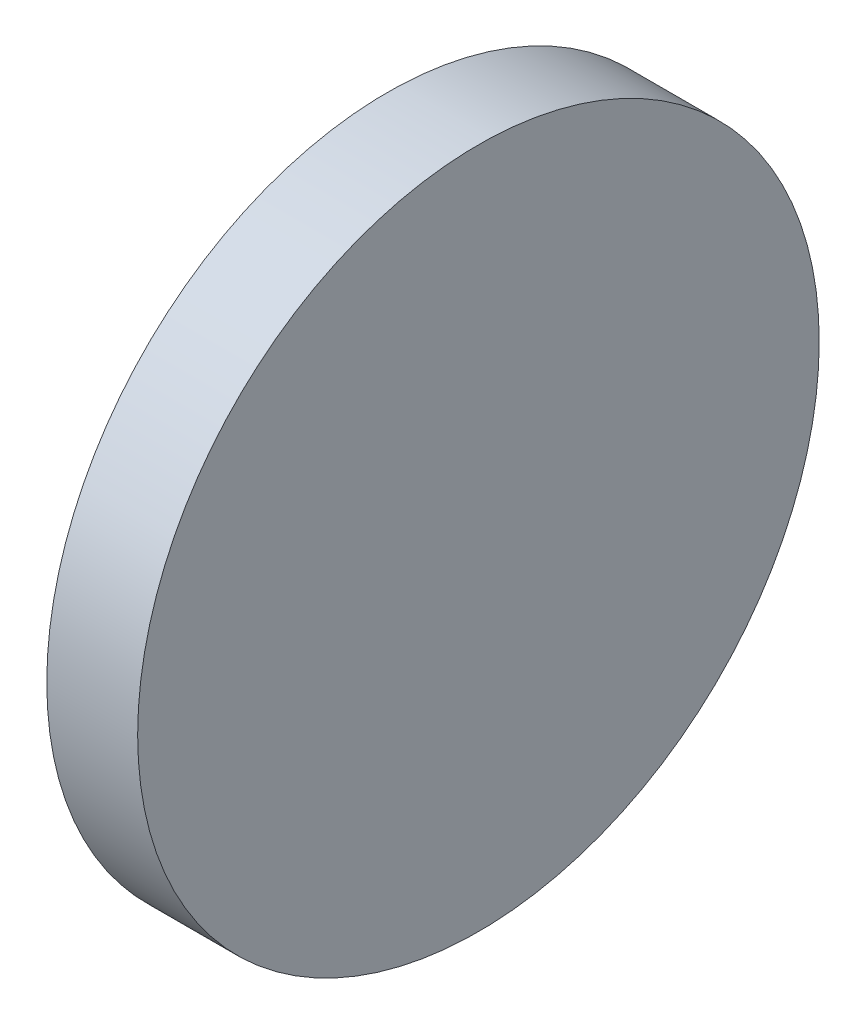
SolidWorks part; units mm, degrees
ref_plane "前视基准面" through (0, 0, 0) normal (0, 0, 1) x (1, 0, 0)
ref_plane "上视基准面" through (0, 0, 0) normal (0, 1, 0) x (1, 0, 0)
ref_plane "右视基准面" through (0, 0, 0) normal (1, 0, 0) x (0, 0, -1)
sketch "草图1" plane through (0, 0, 0) normal (0, 0, 1) x (1, 0, 0)
  line L0 (127.0004, 38.6466) -> (135.3062, 38.6466) construction
  line L1 (130.064, 38.6466) -> (130.064, 46.1466)
  line L2 (130.064, 46.1466) -> (132.064, 46.1466)
  line L3 (132.064, 46.1466) -> (132.064, 38.6466)
  line L4 (132.064, 38.6466) -> (130.064, 38.6466)
revolve "旋转1" add sketch "草图1" angle 360 about L0
